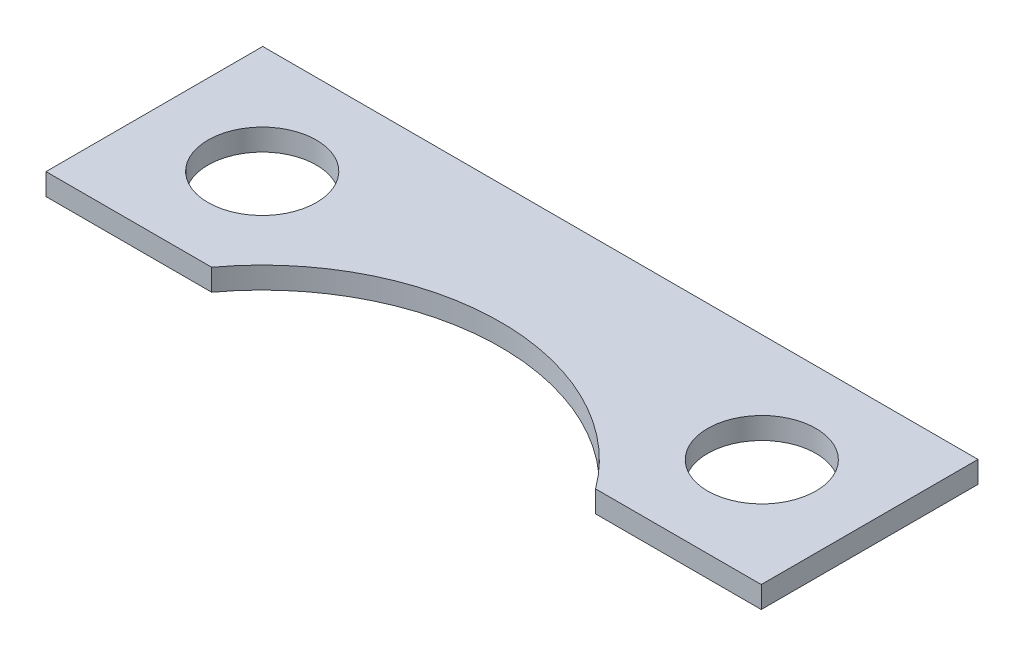
SolidWorks part; units mm, degrees
material "1.6523 (20NiCrMoS2-2)"
ref_plane "Front Plane" through (0, 0, 0) normal (0, 0, 1) x (1, 0, 0)
ref_plane "Top Plane" through (0, 0, 0) normal (0, 1, 0) x (1, 0, 0)
ref_plane "Right Plane" through (0, 0, 0) normal (1, 0, 0) x (0, 0, -1)
sketch "Sketch1" plane through (0, 0, 0) normal (0, 1, 0) x (1, 0, 0)
  line L0 (-11.525, 5) -> (11.525, 5) construction
  line L1 (-16.5, 10) -> (16.5, 10)
  line L2 (-16.5, 10) -> (-16.5, 0)
  line L3 (-16.5, 0) -> (-8.8558, 0)
  line L4 (16.5, 10) -> (16.5, 0)
  line L5 (8.8558, 0) -> (16.5, 0)
  line L6 (-8.8558, 0) -> (8.8558, 0) construction
  arc A0 (8.8558, 0) -> (-8.8558, 0) centre (0, -6.525) ccw
  circle A1 centre (-11.525, 5) radius 2.5
  circle A2 centre (11.525, 5) radius 2.5
  point P11 (0, 5)
  dimension "D4" = 5
  dimension "D5" = 22
  dimension "D1" = 10
  dimension "D2" = 33
  dimension "D3" = 23.05
  dimension "D6" = 11.525
extrude "Boss-Extrude1" add sketch "Sketch1" along normal blind 1
